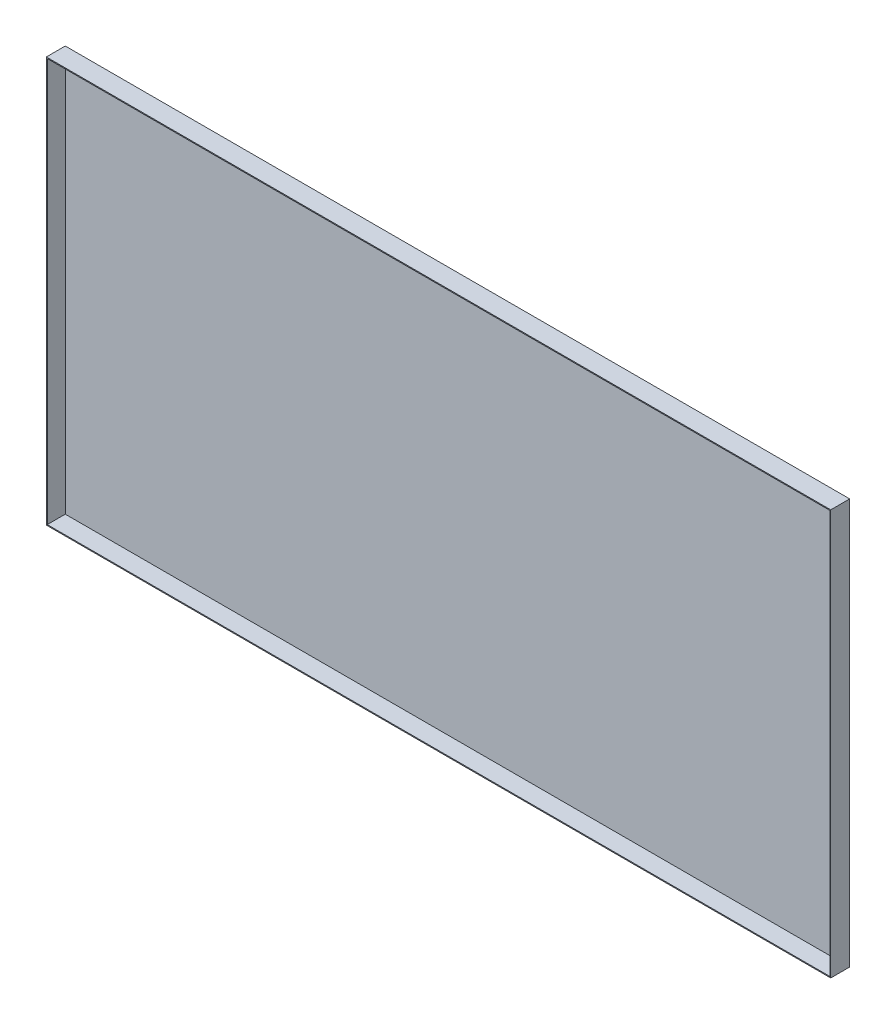
SolidWorks part; units mm, degrees
ref_plane "前视基准面" through (0, 0, 0) normal (0, 0, 1) x (1, 0, 0)
ref_plane "上视基准面" through (0, 0, 0) normal (0, 1, 0) x (1, 0, 0)
ref_plane "右视基准面" through (0, 0, 0) normal (1, 0, 0) x (0, 0, -1)
sketch "草图1" plane through (0, 0, 0) normal (0, 0, 1) x (1, 0, 0)
  line L1 (-414, 214) -> (414, 214)
  line L2 (-414, 214) -> (-414, -214)
  line L3 (-414, -214) -> (414, -214)
  line L4 (414, 214) -> (414, -214)
  line L5 (-414, 214) -> (414, -214) construction
  line L6 (-414, -214) -> (414, 214) construction
  point P0 (0, 0)
  dimension "D1" = 828
  dimension "D2" = 428
extrude "凸台-拉伸1" add sketch "草图1" along normal blind 20
shell "抽壳1" thickness 1
